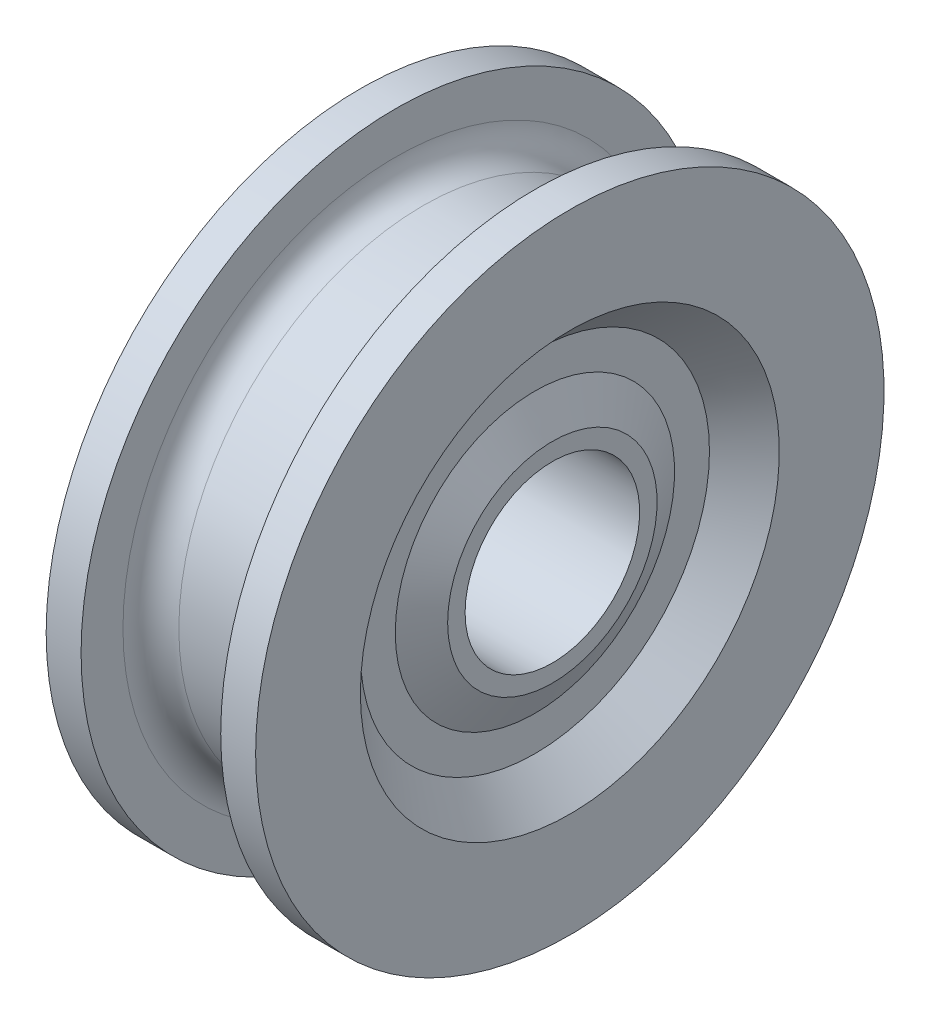
SolidWorks part; units mm, degrees
ref_plane "Plano frontal" through (0, 0, 0) normal (0, 0, 1) x (1, 0, 0)
ref_plane "Plano superior" through (0, 0, 0) normal (0, 1, 0) x (1, 0, 0)
ref_plane "Plano direito" through (0, 0, 0) normal (1, 0, 0) x (0, 0, -1)
sketch "Esboço2" plane through (0, 0, 0) normal (0, 0, 1) x (1, 0, 0)
  line L0 (0, 0) -> (20.3488, 0) construction
  line L1 (1.25, 6.25) -> (13.75, 6.25)
  line L2 (13.75, 6.25) -> (13.75, 7.5)
  line L3 (13.75, 7.5) -> (12.5, 10)
  line L4 (12.5, 10) -> (12.5, 12.5)
  line L5 (12.5, 12.5) -> (15, 15)
  line L6 (15, 15) -> (15, 22.5)
  line L7 (15, 22.5) -> (12.5, 22.5)
  line L8 (12.5, 22.5) -> (12.5, 19.5)
  line L9 (10.5, 17.5) -> (4.5, 17.5)
  line L10 (2.5, 19.5) -> (2.5, 22.5)
  line L11 (2.5, 22.5) -> (0, 22.5)
  line L12 (0, 22.5) -> (0, 15)
  line L13 (0, 15) -> (2.5, 12.5)
  line L14 (2.5, 12.5) -> (2.5, 10)
  line L15 (2.5, 10) -> (1.25, 7.5)
  line L16 (1.25, 7.5) -> (1.25, 6.25)
  arc A8 (12.5, 19.5) -> (10.5, 17.5) centre (10.5, 19.5) cw
  arc A9 (4.5, 17.5) -> (2.5, 19.5) centre (4.5, 19.5) cw
  point P5 (0, 0)
  point P21 (1.25, 7.5)
  dimension "D12" = 30
  dimension "D8" = 2
  dimension "D1" = 12.5
  dimension "D2" = 45
  dimension "D3" = 35
  dimension "D4" = 15
  dimension "D5" = 10
  dimension "D6" = 12.5
  dimension "D7" = 10
  dimension "D9" = 15
  dimension "D10" = 20
  dimension "D11" = 25
  dimension "D13" = 1.25
revolve "Revolução1" add sketch "Esboço2" angle 360 about L0
